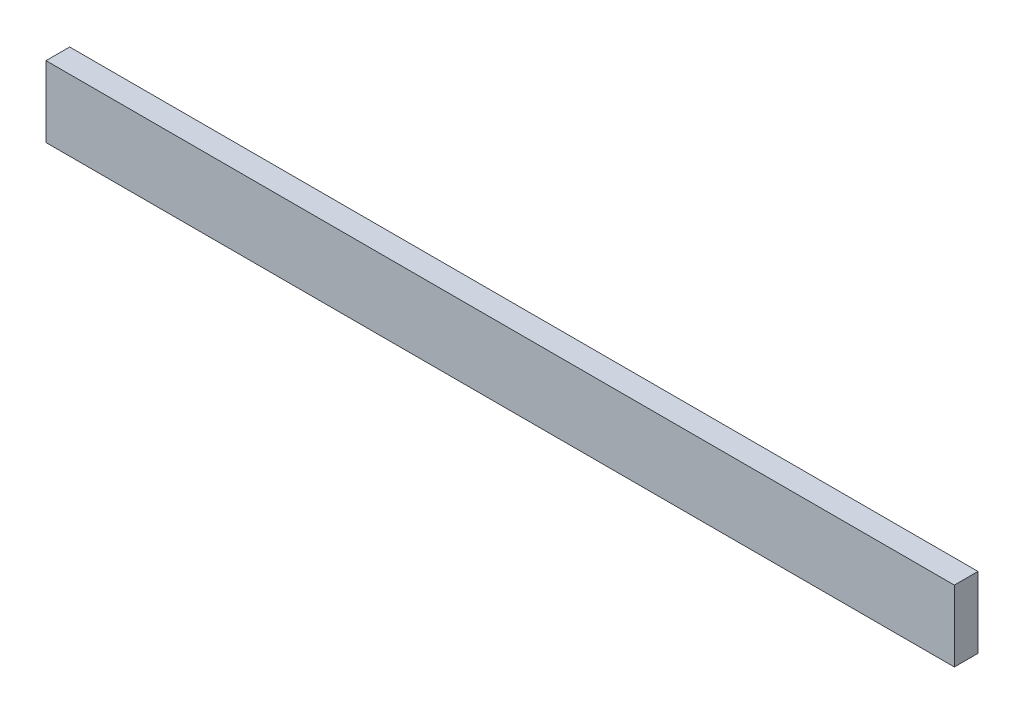
SolidWorks part; units mm, degrees
ref_plane "Front Plane" through (0, 0, 0) normal (0, 0, 1) x (1, 0, 0)
ref_plane "Top Plane" through (0, 0, 0) normal (0, 1, 0) x (1, 0, 0)
ref_plane "Right Plane" through (0, 0, 0) normal (1, 0, 0) x (0, 0, -1)
sketch "Sketch2" plane through (0, 0, 0) normal (0, 0, 1) x (1, 0, 0)
  line L1 (0, 0) -> (243.84, 0)
  line L2 (0, 0) -> (0, 19.05)
  line L3 (0, 19.05) -> (243.84, 19.05)
  line L4 (243.84, 0) -> (243.84, 19.05)
  dimension "D1" = 243.84
  dimension "D2" = 19.05
extrude "Boss-Extrude1" add sketch "Sketch2" along normal blind 6.35
